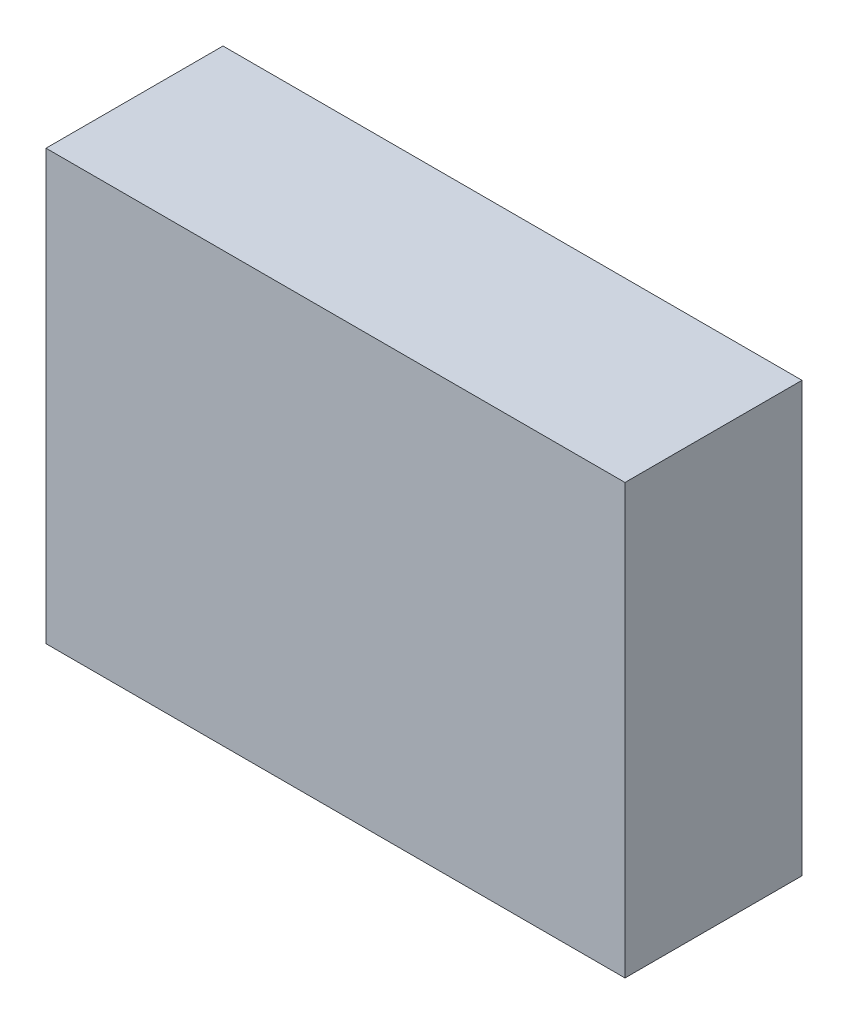
SolidWorks part; units mm, degrees
ref_plane "Front Plane" through (0, 0, 0) normal (0, 0, 1) x (1, 0, 0)
ref_plane "Top Plane" through (0, 0, 0) normal (0, 1, 0) x (1, 0, 0)
ref_plane "Right Plane" through (0, 0, 0) normal (1, 0, 0) x (0, 0, -1)
sketch "Sketch1" plane through (0, 0, 0) normal (0, 0, 1) x (1, 0, 0)
  line L1 (0, 0) -> (49.0683, 0)
  line L2 (0, 0) -> (0, 36.3682)
  line L3 (0, 36.3682) -> (49.0683, 36.3682)
  line L4 (49.0683, 0) -> (49.0683, 36.3682)
extrude "Boss-Extrude1" add sketch "Sketch1" along normal blind 15
